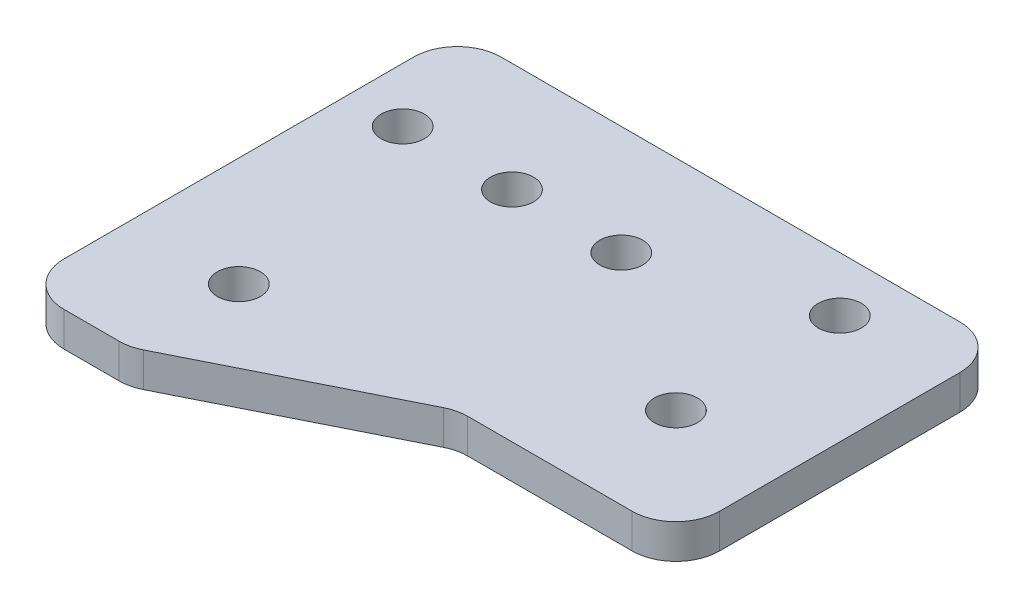
SolidWorks part; units mm, degrees
material "ABS"
ref_plane "Front Plane" through (0, 0, 0) normal (0, 0, 1) x (1, 0, 0)
ref_plane "Top Plane" through (0, 0, 0) normal (0, 1, 0) x (1, 0, 0)
ref_plane "Right Plane" through (0, 0, 0) normal (1, 0, 0) x (0, 0, -1)
sketch "Sketch1" plane through (0, 0, 0) normal (0, -1, 0) x (1, 0, 0)
  line L0 (127, 279.4) -> (101.6, 279.4) construction
  line L1 (101.6, 279.4) -> (101.6, -152.4) construction
  line L3 (127, -152.4) -> (127, 279.4) construction
  line L5 (-101.6, 0) -> (101.6, 0) construction
  line L7 (101.6, 25.4) -> (-101.6, 25.4) construction
  line L8 (127, 279.4) -> (101.6, 279.4)
  line L9 (101.6, 38.1) -> (101.6, 25.4)
  line L10 (63.5, 25.4) -> (63.5, 50.8)
  line L11 (127, 0) -> (127, 38.1)
  line L12 (63.5, 50.8) -> (76.2, 50.8)
  line L13 (63.5, 0) -> (127, 0)
  line L14 (76.2, 50.8) -> (101.6, 38.1)
  line L15 (101.6, 25.4) -> (63.5, 25.4)
  line L16 (63.5, 0) -> (63.5, 25.4)
  line L17 (101.6, 38.1) -> (127, 38.1)
  line L18 (114.3, 38.1) -> (114.3, 0) construction
  line L19 (63.5, 12.7) -> (127, 12.7) construction
  circle A0 centre (76.2, 38.1) radius 2.5
  circle A1 centre (114.3, 6.35) radius 2.5
  circle A2 centre (114.3, 25.4) radius 2.5
  circle A3 centre (69.85, 12.7) radius 2.5
  circle A4 centre (82.55, 12.7) radius 2.5
  circle A5 centre (95.25, 12.7) radius 2.5
  line M6 (101.6, 279.4) -> (101.6, -152.4)
  line M8 (127, -152.4) -> (127, 279.4)
  dimension "D3" = 5
  dimension "D7" = 5
  dimension "D10" = 5
  dimension "D1" = 38.1
  dimension "D2" = 38.1
  dimension "D4" = 25.4
  dimension "D5" = 25.4
  dimension "D6" = 12.7
  dimension "D8" = 6.35
  dimension "D11" = 6.35
  dimension "D9" = 2
  dimension "D12" = 3
extrude "Boss-Extrude1" add sketch "Sketch1" along normal blind 4 contours L16 L13 L15 M6 | L17 L13 M6 M8 | L15 L14 L12 L10 A0 M6
fillet "Fillet1" radius 5.08 6 edges at (76.2, -2, 50.8) (101.6, -2, 38.1) (127, -2, 38.1) (127, -2, 0) (63.5, -2, 0) (63.5, -2, 50.8)
